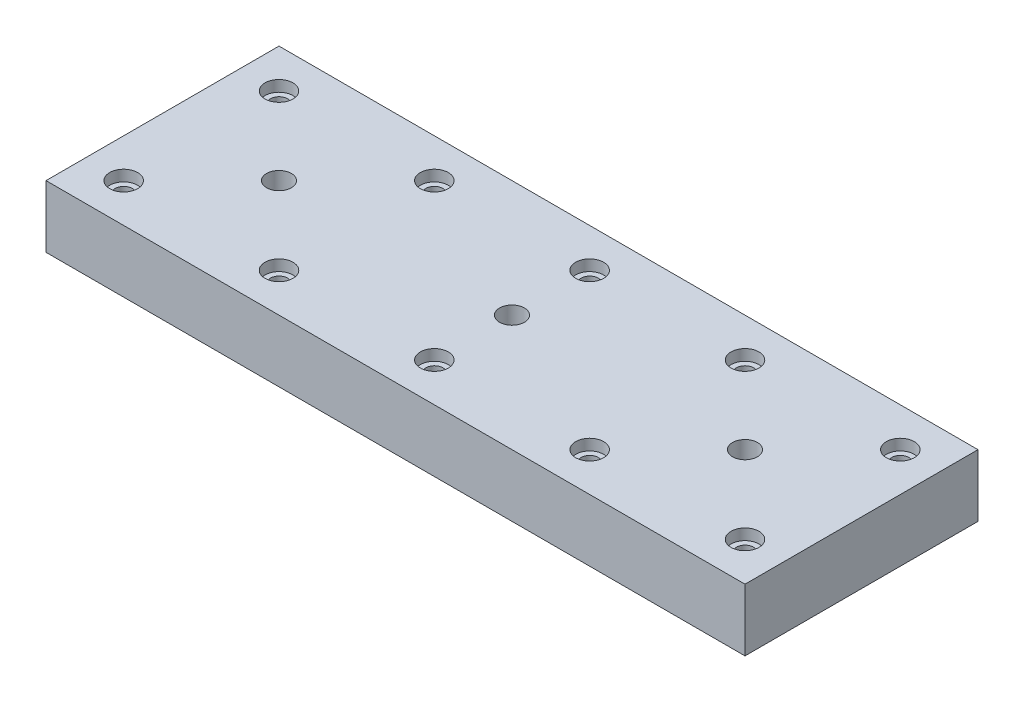
SolidWorks part; units mm, degrees
material "Liga 6061"
ref_plane "Plano frontal" through (0, 0, 0) normal (0, 0, 1) x (1, 0, 0)
ref_plane "Plano superior" through (0, 0, 0) normal (0, 1, 0) x (1, 0, 0)
ref_plane "Plano direito" through (0, 0, 0) normal (1, 0, 0) x (0, 0, -1)
sketch "Esboço1" plane through (0, 0, 0) normal (0, 1, 0) x (1, 0, 0)
  line L1 (-225, -75) -> (225, -75)
  line L2 (-225, -75) -> (-225, 75)
  line L3 (-225, 75) -> (225, 75)
  line L4 (225, -75) -> (225, 75)
  line L5 (-225, -75) -> (225, 75) construction
  line L6 (-225, 75) -> (225, -75) construction
  point P0 (0, 0)
  dimension "D1" = 450
  dimension "D2" = 150
extrude "Ressalto-extrusão1" add sketch "Esboço1" along normal blind 40
hole_wizard "Rebaixo para parafuso Allen sextavado de M101" positions "Esboço3" profile "Esboço2" counterbore size "M10" standard "DIN" end condition up to next
sketch "Esboço3" plane through (0, 40, 0) normal (0, 1, 0) x (1, 0, 0)
  line L0 (-225, 75) -> (-225, -75) construction
  point P0 (-200, 50)
  point P12 (-100, 50)
  point P13 (0, 50)
  point P14 (100, 50)
  point P15 (200, 50)
  point P21 (-100, -50)
  point P22 (0, -50)
  point P23 (100, -50)
  point P24 (200, -50)
  point P30 (-200, -50)
  dimension "D1" = 25
  dimension "D2" = 50
  dimension "D3" = 5
  dimension "D4" = 2
sketch "Esboço2" plane through (-200, 40, -50) normal (1, 0, 0) x (0, 0, 1)
  line L0 (0, 0) -> (0, 40)
  line L1 (0, 40) -> (5.5, 40)
  line L3 (5.5, 40) -> (5.5, 7.1)
  line L4 (5.5, 7.1) -> (9, 7.1)
  line L5 (9, 7.1) -> (9, 0)
  line L7 (9, 0) -> (0, 0)
  line L11 (0, -6.35) -> (0, 107.95) construction
  dimension "Thru Hole Dia." = 11
  dimension "Thru Hole Depth" = 40
  dimension "C'Bore Dia." = 18
  dimension "C'Bore Depth" = 7.1
hole_wizard "Furo roscado de M18x2.0" positions "Esboço7" profile "Esboço6" tap size "M18x2.0" standard "Ansi Metric" end condition up to next
sketch "Esboço7" plane through (0, 40, 0) normal (0, 1, 0) x (1, 0, 0)
  line L0 (-225, 75) -> (-225, -75) construction
  line L1 (0, 0) -> (-225, 0) construction
  point P0 (0, 0)
  point P5 (-225, 0)
  point P71 (150, 0)
  point P72 (0, 0)
  point P73 (-150, 0)
  dimension "D2" = 2
  dimension "D1" = 2
sketch "Esboço6" plane through (0, 40, 0) normal (1, 0, 0) x (0, 0, 1)
  line L0 (0, 0) -> (0, 40)
  line L1 (0, 40) -> (8, 40)
  line L2 (8, 40) -> (8, 0)
  line L5 (8, 0) -> (0, 0)
  line L11 (0, -6.35) -> (0, 107.95) construction
  dimension "Thru Tap Drill Dia." = 16
  dimension "Thru Tap Drill Depth" = 40
cosmetic thread "Rosca de furo12"
cosmetic thread "Rosca de furo37"
cosmetic thread "Rosca de furo38"
cosmetic thread "Rosca de furo39"
hole_wizard "Furo roscado de M16x2.0" [suppressed] positions "Esboço9" profile "Esboço8" tap size "M16x2.0" standard "Ansi Metric"
sketch "Esboço9" plane through (0, 40, 0) normal (0, 1, 0) x (1, 0, 0)
  line L0 (-1020, 0) -> (-1050, 0) construction
  line L1 (-1050, 100) -> (-1050, -100) construction
  line L2 (1020, 0) -> (1050, 0) construction
  line L3 (1050, -100) -> (1050, 100) construction
  point P0 (-1020, 0)
  point P13 (-900, 0)
  point P14 (-780, 0)
  point P15 (-660, 0)
  point P16 (-540, 0)
  point P17 (-420, 0)
  point P18 (-300, 0)
  point P19 (-180, 0)
  point P20 (-60, 0)
  point P21 (60, 0)
  point P22 (180, 0)
  point P23 (300, 0)
  point P24 (420, 0)
  point P25 (540, 0)
  point P26 (660, 0)
  point P27 (780, 0)
  point P28 (900, 0)
  point P29 (1020, 0)
  dimension "D1" = 18
sketch "Esboço8" plane through (-1020, 40, 0) normal (1, 0, 0) x (0, 0, 1)
  line L0 (0, 0) -> (0, 40)
  line L1 (0, 40) -> (7, 40)
  line L2 (7, 40) -> (7, 0)
  line L5 (7, 0) -> (0, 0)
  line L11 (0, -6.35) -> (0, 107.95) construction
  dimension "Thru Tap Drill Dia." = 14
  dimension "Thru Tap Drill Depth" = 40
cosmetic thread "Rosca de furo19" [suppressed] parameters "D2"=16
cosmetic thread "Rosca de furo20" [suppressed] parameters "D2"=16
cosmetic thread "Rosca de furo21" [suppressed] parameters "D2"=16
cosmetic thread "Rosca de furo22" [suppressed] parameters "D2"=16
cosmetic thread "Rosca de furo23" [suppressed] parameters "D2"=16
cosmetic thread "Rosca de furo24" [suppressed] parameters "D2"=16
cosmetic thread "Rosca de furo25" [suppressed] parameters "D2"=16
cosmetic thread "Rosca de furo26" [suppressed] parameters "D2"=16
cosmetic thread "Rosca de furo27" [suppressed] parameters "D2"=16
cosmetic thread "Rosca de furo28" [suppressed] parameters "D2"=16
cosmetic thread "Rosca de furo29" [suppressed] parameters "D2"=16
cosmetic thread "Rosca de furo30" [suppressed] parameters "D2"=16
cosmetic thread "Rosca de furo31" [suppressed] parameters "D2"=16
cosmetic thread "Rosca de furo32" [suppressed] parameters "D2"=16
cosmetic thread "Rosca de furo33" [suppressed] parameters "D2"=16
cosmetic thread "Rosca de furo34" [suppressed] parameters "D2"=16
cosmetic thread "Rosca de furo35" [suppressed] parameters "D2"=16
cosmetic thread "Rosca de furo36" [suppressed] parameters "D2"=16
